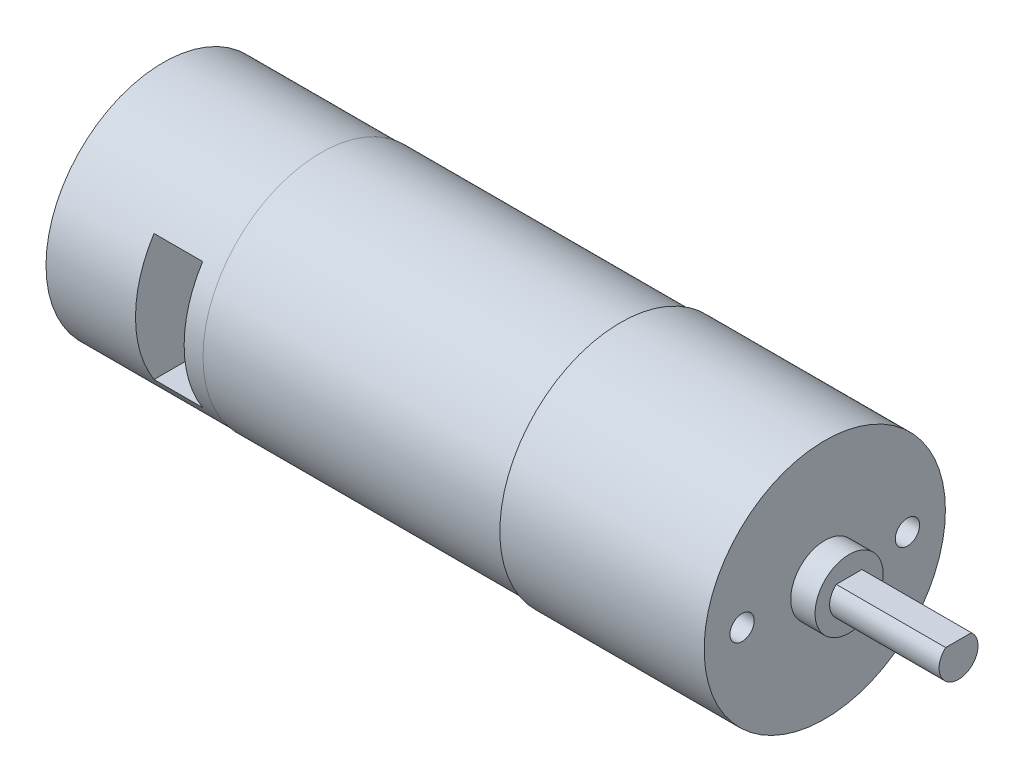
SolidWorks part; units mm, degrees
ref_plane "Front Plane" through (0, 0, 0) normal (0, 0, 1) x (1, 0, 0)
ref_plane "Top Plane" through (0, 0, 0) normal (0, 1, 0) x (1, 0, 0)
ref_plane "Right Plane" through (0, 0, 0) normal (1, 0, 0) x (0, 0, -1)
sketch "Sketch1" plane through (0, 0, 0) normal (1, 0, 0) x (0, 0, -1)
  circle A0 centre (0, 0) radius 12.4
  dimension "D1" = 24.8
extrude "Boss-Extrude2" add sketch "Sketch1" against normal blind 21 contours A0
sketch "Sketch3" plane through (-21, 0, 0) normal (-1, 0, 0) x (0, 0, 1)
  circle A2 centre (0, 0) radius 12.115
  dimension "D1" = 24.23
extrude "Boss-Extrude3" add sketch "Sketch3" along normal blind 30.8
sketch "Sketch4" plane through (-51.8, 0, 0) normal (-1, 0, 0) x (0, 0, 1)
  circle A3 centre (0, 0) radius 12.05
  dimension "D1" = 24.1
extrude "Boss-Extrude4" add sketch "Sketch4" along normal blind 16.2
sketch "Sketch5" plane through (0, 0, 0) normal (1, 0, 0) x (0, 0, -1)
  circle A0 centre (0, 0) radius 3.5
  dimension "D1" = 7
extrude "Boss-Extrude5" add sketch "Sketch5" along normal blind 2.5
sketch "Sketch6" plane through (2.5, 0, 0) normal (1, 0, 0) x (0, 0, -1)
  line L0 (-1.3229, 1.5) -> (1.3229, 1.5)
  arc A0 (-1.3229, 1.5) -> (1.3229, 1.5) centre (0, 0) ccw
  point P1 (0, -2)
  dimension "D1" = 4
  dimension "D2" = 3.5
extrude "Boss-Extrude6" add sketch "Sketch6" along normal blind 11.25
hole_wizard "M3x0.5 Tapped Hole1" positions "Sketch7" profile "Sketch8" tap size "M3x0.5" standard "ANSI Metric"
sketch "Sketch7" plane through (0, 0, 0) normal (1, 0, 0) x (0, 0, -1)
  circle A0 centre (0, 0) radius 8.5 construction
  point P0 (-8.5, 0)
  point P2 (8.5, 0)
  dimension "D1" = 17
sketch "Sketch8" plane through (0, 0, 8.5) normal (0, 1, 0) x (0, 0, -1)
  line L0 (0, 0) -> (0, 4.7511)
  line L1 (0, 4.7511) -> (1.25, 4)
  line L2 (1.25, 4) -> (1.25, 0)
  line L5 (1.25, 0) -> (0, 0)
  line L10 (0, 4.7511) -> (-1.25, 4) construction
  line L11 (0, -6.35) -> (0, 107.95) construction
  dimension "Tap Drill Dia." = 2.5
  dimension "Tap Drill Depth" = 4
  dimension "Drill Angle" = 118
cosmetic thread "Hole Thread1" parameters "D1"=6, "D2"=3
cosmetic thread "Hole Thread2" parameters "D1"=6, "D2"=3
sketch "Sketch9" plane through (0, 0, 0) normal (0, 0, 1) x (1, 0, 0)
  line L6 (-58.8, 6.5) -> (-53.8, 6.5)
  line L7 (-58.8, 6.5) -> (-58.8, -6.5)
  line L8 (-58.8, -6.5) -> (-53.8, -6.5)
  line L9 (-53.8, 6.5) -> (-53.8, -6.5)
  line L10 (-51.8, 12.05) -> (-51.8, -12.05) construction
  point P4 (-53.8, 0)
  dimension "D1" = 2
  dimension "D2" = 5
  dimension "D3" = 13
extrude "Cut-Extrude2" cut sketch "Sketch9" along normal through all
